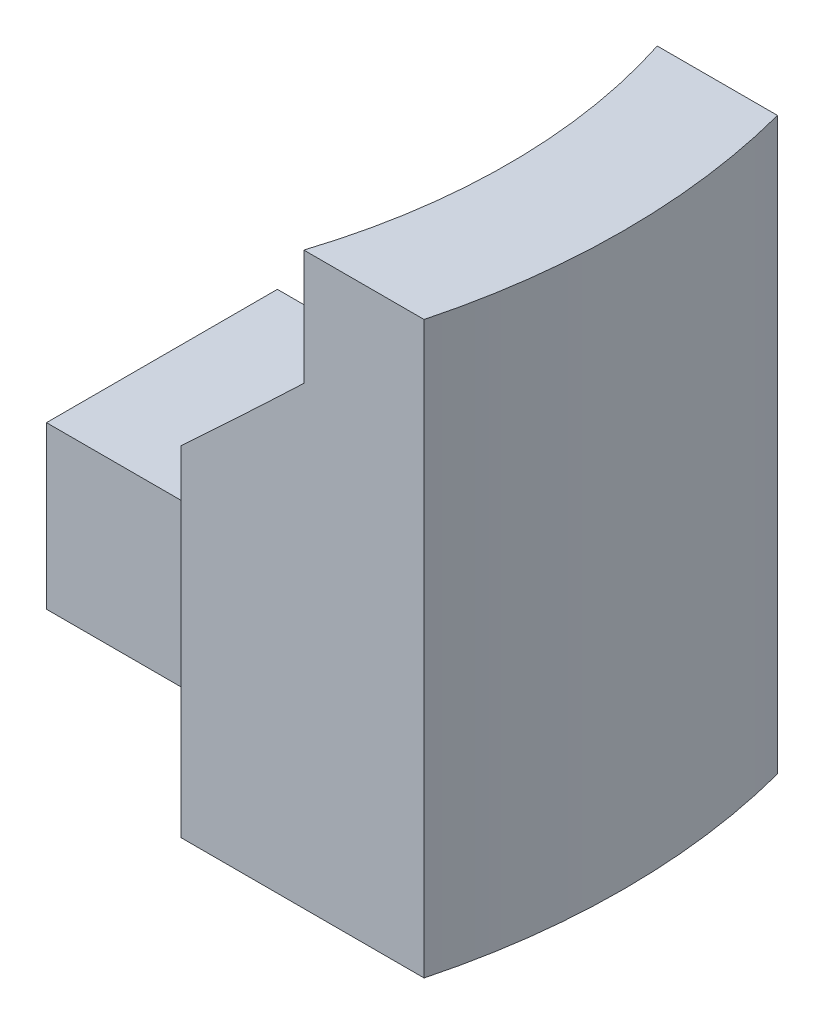
SolidWorks part; units mm, degrees
ref_plane "Front Plane" through (0, 0, 0) normal (0, 0, 1) x (1, 0, 0)
ref_plane "Top Plane" through (0, 0, 0) normal (0, 1, 0) x (1, 0, 0)
ref_plane "Right Plane" through (0, 0, 0) normal (1, 0, 0) x (0, 0, -1)
sketch "Sketch2" plane through (0, 0, 0) normal (0, 0, 1) x (1, 0, 0)
  line L0 (0, 0) -> (5, 0)
  line L1 (5, 0) -> (5, 12.35)
  line L2 (5, 12.35) -> (2.5, 12.35)
  line L3 (2.5, 12.35) -> (2.5, 9.85)
  line L4 (2.5, 9.85) -> (0, 7.35)
  line L5 (0, 7.35) -> (0, 0)
  line L6 (-10, 0) -> (-10, 17.2703) construction
  point P9 (5, 14.6837)
  dimension "D1" = 7.35
  dimension "D2" = 2.5
  dimension "D3" = 45
  dimension "D4" = 2.5
  dimension "D5" = 10
  dimension "D6" = 2.5
revolve "Revolve1" add sketch "Sketch2" angle 45 mid plane about L6
sketch "Sketch3" plane through (0, 0, 0) normal (1, 0, 0) x (0, 0, -1)
  line L0 (-3.8268, 0) -> (3.8268, 0) construction
  line L1 (2.5, 0) -> (-2.5, 0)
  line L2 (2.5, 0) -> (2.5, 5)
  line L3 (2.5, 5) -> (-2.5, 5)
  line L4 (-2.5, 0) -> (-2.5, 5)
  line L5 (2.5, 0) -> (-2.5, 5) construction
  line L6 (2.5, 5) -> (-2.5, 0) construction
  point P0 (0, 2.5)
  point P5 (0, 0)
  dimension "D1" = 5
extrude "Boss-Extrude2" add sketch "Sketch3" against normal blind 5
chamfer "Chamfer2" distance 1.5 angle 45 2 edges at (-2.6588, 0, -2.5) (-2.6588, 0, 2.5)
sketch "Sketch4" plane through (0, 0, 0) normal (0, -1, 0) x (1, 0, 0)
  line L0 (-0.7612, 3.8268) -> (4.5036, 3.8268)
  line L1 (-0.7612, -3.8268) -> (4.5036, -3.8268)
  line L2 (-0.7612, 3.8268) -> (3.8582, 5.7403) construction
  line L3 (-0.7612, -3.8268) -> (3.8582, -5.7403) construction
  line L4 (-0.7612, 3.8268) -> (3.8582, 5.7403)
  line L5 (-0.7612, -3.8268) -> (3.8582, -5.7403)
  arc A0 (3.8582, -5.7403) -> (3.8582, 5.7403) centre (-10, 0) ccw construction
  arc A1 (3.8582, -5.7403) -> (4.5036, -3.8268) centre (-10, 0) ccw
  arc A2 (4.5036, 3.8268) -> (3.8582, 5.7403) centre (-10, 0) ccw
  point P9 (4.5036, -3.8268)
extrude "Cut-Extrude1" cut sketch "Sketch4" against normal through all both and the other way through all
